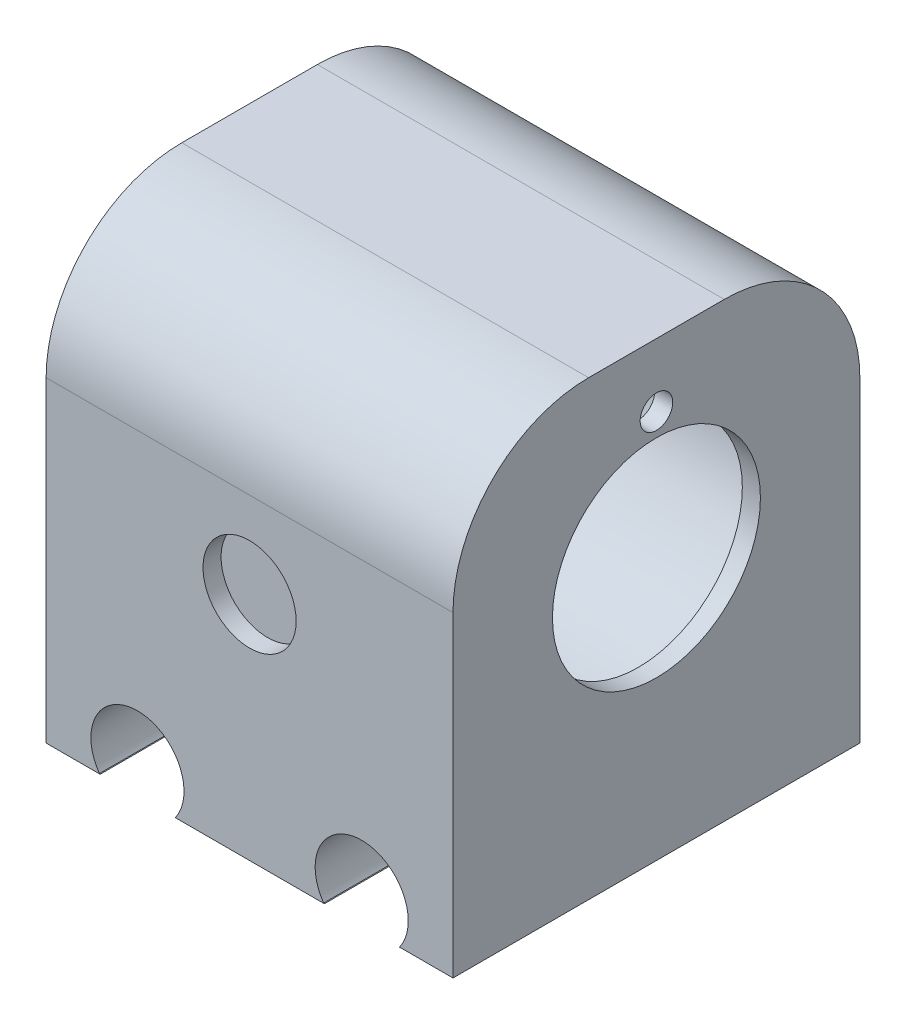
SolidWorks part; units mm, degrees
ref_plane "Front Plane" through (0, 0, 0) normal (0, 0, 1) x (1, 0, 0)
ref_plane "Top Plane" through (0, 0, 0) normal (0, 1, 0) x (1, 0, 0)
ref_plane "Right Plane" through (0, 0, 0) normal (1, 0, 0) x (0, 0, -1)
sketch "Sketch1" plane through (0, 0, 0) normal (0, 0, 1) x (1, 0, 0)
  line L1 (-14.2634, 22.0982) -> (30.7366, 22.0982)
  line L2 (-14.2634, 22.0982) -> (-14.2634, -27.9018)
  line L3 (-14.2634, -27.9018) -> (30.7366, -27.9018)
  line L4 (30.7366, 22.0982) -> (30.7366, -27.9018)
  dimension "D1" = 50
  dimension "D2" = 45
extrude "Boss-Extrude1" add sketch "Sketch1" along normal blind 45
sketch "Sketch2" plane through (0, 0, 45) normal (0, 0, 1) x (1, 0, 0)
  line L0 (-14.2634, -27.9018) -> (30.7366, -27.9018) construction
  line L1 (-14.2634, 22.0982) -> (-14.2634, -27.9018) construction
  circle A0 centre (-4.1634, -24.9018) radius 5.2
  circle A1 centre (20.6366, -24.9018) radius 5.2
  dimension "D1" = 3
  dimension "D3" = 10.1
  dimension "D2" = 2
extrude "Cut-Extrude1" cut sketch "Sketch2" against normal blind 45
sketch "Sketch9" plane through (0, 0, 45) normal (0, 0, 1) x (1, 0, 0)
  line L0 (8.2366, 22.0982) -> (8.2366, -2.4018) construction
  line L1 (30.7366, 22.0982) -> (-14.2634, 22.0982) construction
  circle A0 centre (8.2366, -2.4018) radius 5.15
  dimension "D1" = 24.5
extrude "Cut-Extrude6" cut sketch "Sketch9" against normal blind 2
sketch "Sketch10" plane through (0, 0, 0) normal (0, 0, -1) x (-1, 0, 0)
  line L0 (-8.2366, 22.0982) -> (-8.2366, -2.4018) construction
  line L1 (-30.7366, 22.0982) -> (14.2634, 22.0982) construction
  circle A0 centre (-8.2366, -2.4018) radius 5.15
  dimension "D1" = 24.5
extrude "Cut-Extrude7" cut sketch "Sketch10" against normal blind 2
sketch "Sketch12" plane through (-14.2634, 0, 0) normal (-1, 0, 0) x (0, 0, 1)
  line L0 (22.5, 22.0982) -> (22.5, -7.2504) construction
  line L1 (45, 22.0982) -> (0, 22.0982) construction
  line L2 (0, -16.4263) -> (45, -16.4263) construction
  line L3 (0, 22.0982) -> (0, -27.9018) construction
  line L4 (45, 22.0982) -> (45, -27.9018) construction
  circle A0 centre (22.5, 1.0982) radius 18.375
  dimension "D1" = 36.75
extrude "Cut-Extrude8" cut sketch "Sketch12" against normal blind 45
sketch "Sketch13" plane through (-14.2634, 0, 0) normal (-1, 0, 0) x (0, 0, 1)
  line L0 (45, 22.0982) -> (45, -27.9018) construction
  line L1 (0, 22.0982) -> (45, 22.0982)
  line L2 (0, 22.0982) -> (0, 15.4307)
  line L3 (0, 15.4307) -> (45, 15.4307)
  line L4 (45, 22.0982) -> (45, 15.4307)
extrude "Cut-Extrude9" cut sketch "Sketch13" against normal blind 46
sketch "Sketch14" plane through (-14.2634, 0, 0) normal (-1, 0, 0) x (0, 0, 1)
  line L1 (0, 15.4307) -> (45, 15.4307)
  line L2 (0, 15.4307) -> (0, 22.0982)
  line L3 (0, 22.0982) -> (45, 22.0982)
  line L4 (45, 15.4307) -> (45, 22.0982)
  dimension "D1" = 45
extrude "Boss-Extrude2" add sketch "Sketch14" against normal blind 45
sketch "Sketch15" plane through (-14.2634, 0, 0) normal (-1, 0, 0) x (0, 0, 1)
  circle A0 centre (22.5, 1.0982) radius 18.375
extrude "Cut-Extrude10" cut sketch "Sketch15" against normal blind 45
fillet "Fillet1" radius 15 2 edges at (8.2366, 22.0982, 45) (8.2366, 22.0982, 0)
sketch "Sketch16" plane through (30.7366, 0, 0) normal (1, 0, 0) x (0, 0, -1)
  circle A0 centre (-22.5, 1.0982) radius 18.375
extrude "Boss-Extrude3" add sketch "Sketch16" against normal blind 2
sketch "Sketch17" plane through (30.7366, 0, 0) normal (1, 0, 0) x (0, 0, -1)
  circle A0 centre (-22.5, 1.0982) radius 11.5
extrude "Cut-Extrude11" cut sketch "Sketch17" against normal blind 2
sketch "Sketch18" plane through (30.7366, 0, 0) normal (1, 0, 0) x (0, 0, -1)
  circle A0 centre (-22.5, 1.0982) radius 14 construction
  circle A1 centre (-22.5, 15.0982) radius 1.8
extrude "Cut-Extrude12" cut sketch "Sketch18" against normal blind 2
sketch "Sketch19" plane through (0, 0, 45) normal (0, 0, 1) x (1, 0, 0)
  line L0 (0.0431, -27.8729) -> (0.0227, -27.9018)
  line L1 (0.0227, -27.9018) -> (0.084, -27.9018)
  line L2 (-8.3699, -27.8729) -> (-8.2868, -27.9018)
  line L3 (-8.2868, -27.9018) -> (-8.4107, -27.9018)
  line L4 (16.4301, -27.8729) -> (16.5166, -27.9018)
  line L5 (16.5166, -27.9018) -> (16.3893, -27.9018)
  line L6 (24.8431, -27.8729) -> (24.8227, -27.9018)
  line L7 (24.8227, -27.9018) -> (24.884, -27.9018)
  arc A0 (0.084, -27.9018) -> (-8.4107, -27.9018) centre (-4.1634, -24.9018) ccw construction
  arc A1 (0.084, -27.9018) -> (-8.4107, -27.9018) centre (-4.1634, -24.9018) ccw
  arc A3 (24.884, -27.9018) -> (16.3893, -27.9018) centre (20.6366, -24.9018) ccw construction
  arc A4 (24.8431, -27.8729) -> (16.4301, -27.8729) centre (20.6366, -24.9018) ccw
  arc A5 (24.8431, -27.8729) -> (16.4301, -27.8729) centre (20.6366, -24.9018) ccw
  arc A6 (24.884, -27.9018) -> (16.3893, -27.9018) centre (20.6366, -24.9018) ccw
  arc A13 (0.0431, -27.8729) -> (-8.3699, -27.8729) centre (-4.1634, -24.9018) ccw
  arc A14 (0.0431, -27.8729) -> (-8.3699, -27.8729) centre (-4.1634, -24.9018) ccw
  dimension "D1" = 0.05
  dimension "D2" = 0.05
extrude "Boss-Extrude4" add sketch "Sketch19" against normal blind 45
